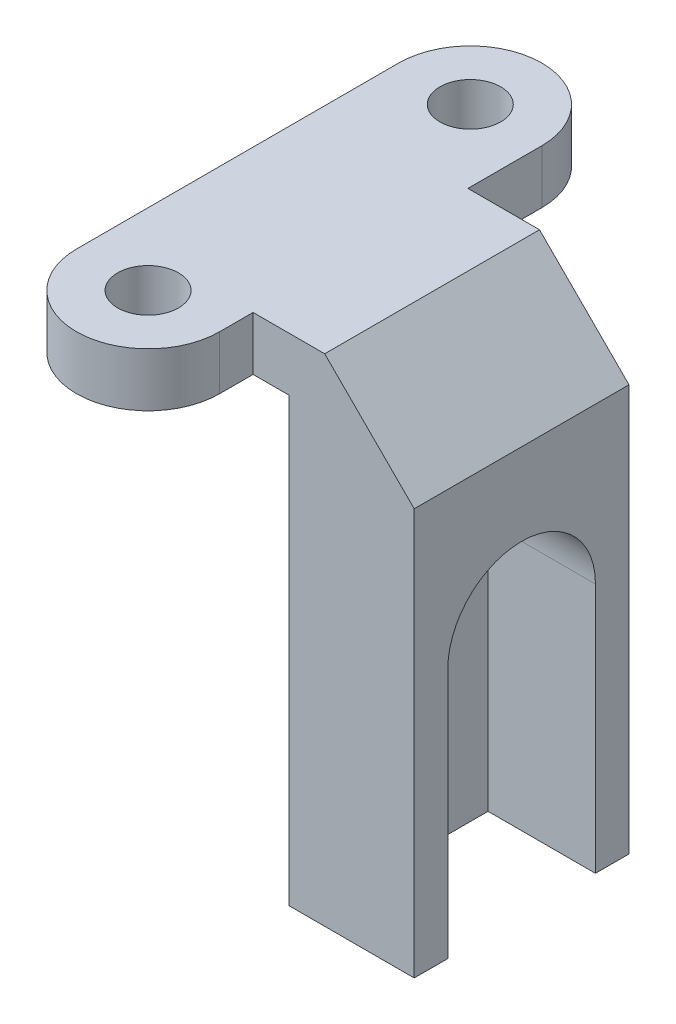
SolidWorks part; units mm, degrees
ref_plane "Front Plane" through (0, 0, 0) normal (0, 0, 1) x (1, 0, 0)
ref_plane "Top Plane" through (0, 0, 0) normal (0, 1, 0) x (1, 0, 0)
ref_plane "Right Plane" through (0, 0, 0) normal (1, 0, 0) x (0, 0, -1)
sketch "Sketch1" plane through (0, 0, 0) normal (0, 1, 0) x (1, 0, 0)
  line L0 (0, 9) -> (0, -9) construction
  line L1 (4, -9) -> (4, -7.1324)
  line L2 (-4, 4.8676) -> (-4, -9)
  line L3 (4, -7.1324) -> (13, -7.1324)
  line L4 (13, 4.8676) -> (4, 4.8676)
  line L5 (13, 4.8676) -> (13, -7.1324)
  line L6 (-4, 4.8676) -> (-4, 9)
  line L7 (4, 4.8676) -> (-4, 4.8676) construction
  line L8 (13, -1.1324) -> (0.235, -1.1324) construction
  line L9 (4, -7.1324) -> (4, 4.8676) construction
  line L10 (4, 4.8676) -> (4, 9)
  arc A0 (4, 9) -> (-4, 9) centre (0, 9) ccw
  arc A1 (-4, -9) -> (4, -9) centre (0, -9) ccw
  point P2 (6.1244, 5.9625)
  point P4 (0, 0)
  point P16 (4, 6.4723)
  point P17 (4, 4.3906)
  point P19 (4, 6.7697)
  dimension "D1" = 18
  dimension "D2" = 8
  dimension "D3" = 13
  dimension "D4" = 12
extrude "Boss-Extrude1" add sketch "Sketch1" along normal blind 3
hole_wizard "M3 Clearance Hole1" positions "Sketch4" profile "Sketch5" hole size "M3" standard "ANSI Metric"
sketch "Sketch4" plane through (0, 3, 0) normal (0, 1, 0) x (1, 0, 0)
  point P0 (0, -9)
  point P3 (0, 9)
  dimension "D1" = 18
sketch "Sketch5" plane through (0, 3, 9) normal (1, 0, 0) x (0, 0, 1)
  line L0 (0, 0) -> (0, 11.0215)
  line L1 (0, 11.0215) -> (1.7, 10)
  line L2 (1.7, 10) -> (1.7, 0)
  line L5 (1.7, 0) -> (0, 0)
  line L10 (0, 11.0215) -> (-1.7, 10) construction
  line L11 (0, -6.35) -> (0, 107.95) construction
  dimension "Hole Dia." = 3.4
  dimension "Hole Depth" = 10
  dimension "Drill Angle" = 118
sketch "Sketch2" plane through (0, 0, 0) normal (0, -1, 0) x (1, 0, 0)
  line L0 (6, 7.1324) -> (6, -4.8676)
  line L5 (-4, 9) -> (-4, -9)
  line L6 (4, -4.8676) -> (13, -4.8676)
  line L7 (13, -4.8676) -> (13, 7.1324)
  line L8 (13, 7.1324) -> (4, 7.1324)
  line L9 (4, 7.1324) -> (4, 9)
  line L11 (6, -4.8676) -> (13, -4.8676)
  line L12 (13, -4.8676) -> (13, 7.1324)
  line L13 (13, 7.1324) -> (6, 7.1324)
  line L17 (4, -9) -> (4, -4.8676)
  arc A2 (-4, -9) -> (4, -9) centre (0, -9) ccw
  arc A3 (4, 9) -> (-4, 9) centre (0, 9) ccw
  dimension "D2" = 7
  dimension "D1" = 0
extrude "Boss-Extrude2" add sketch "Sketch2" along normal blind 24.7
sketch "Sketch3" plane through (13, 0, 0) normal (1, 0, 0) x (0, 0, -1)
  line L0 (-5.1324, -24.7) -> (-5.1324, -10.7) construction
  line L2 (2.8676, -10.7) -> (2.8676, -24.7) construction
  line L3 (4.8676, -24.7) -> (-7.1324, -24.7) construction
  line L4 (2.9926, -24.7) -> (-5.2574, -24.7)
  line L7 (4.8676, 3) -> (4.8676, -24.7) construction
  line L8 (-5.2574, -24.7) -> (-5.2574, -10.7)
  line L9 (2.9926, -10.7) -> (2.9926, -24.7)
  arc A0 (-5.1324, -10.7) -> (2.8676, -10.7) centre (-1.1324, -10.7) cw construction
  arc A1 (-5.2574, -10.7) -> (2.9926, -10.7) centre (-1.1324, -10.7) cw
  dimension "D1" = 8
  dimension "D2" = 2
  dimension "D3" = 14
  dimension "D4" = 0.125
extrude "Cut-Extrude1" cut sketch "Sketch3" against normal blind 6
fillet "Fillet1" [suppressed] radius 2
chamfer "Chamfer3" distance 5 angle 45 1 edges at (13, 3, 1.1324)
